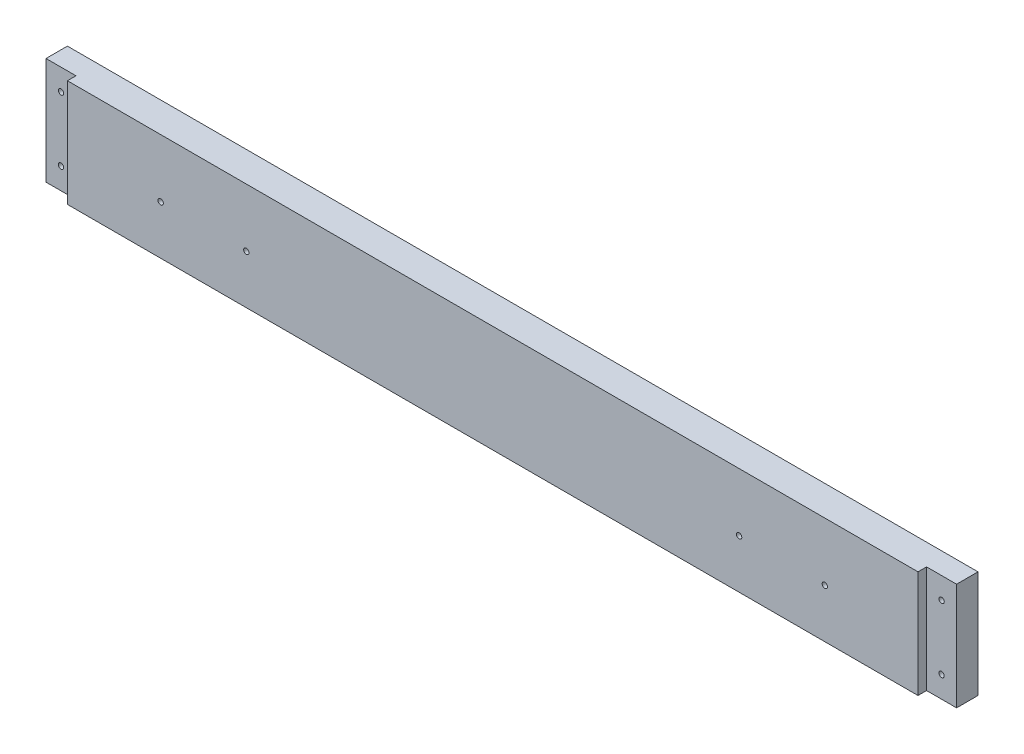
SolidWorks part; units mm, degrees
material "Pine"
ref_plane "Front Plane" through (0, 0, 0) normal (0, 0, 1) x (1, 0, 0)
ref_plane "Top Plane" through (0, 0, 0) normal (0, 1, 0) x (1, 0, 0)
ref_plane "Right Plane" through (0, 0, 0) normal (1, 0, 0) x (0, 0, -1)
sketch "Sketch1" plane through (0, 0, 0) normal (0, 0, 1) x (1, 0, 0)
  line L0 (8932.6508, -5243.5125) -> (10226.1458, -5243.5125)
  line L1 (9086.3208, -4722.0918) -> (10222.9708, -4853.7812)
  line L2 (8914.8708, -6342.0625) -> (10197.5708, -6342.0625)
  line L3 (8914.8708, -5808.6625) -> (10197.5708, -5808.6625)
  line L4 (8919.6333, -5253.0375) -> (10218.2083, -5253.0375)
  line L5 (9134.2633, -4656.1375) -> (9134.2633, -4638.3575)
  line L6 (9091.0833, -4638.3575) -> (9134.2633, -4638.3575)
  line L7 (9091.0833, -4567.2375) -> (9091.0833, -4638.3575)
  line L8 (9134.2633, -4656.1375) -> (9581.3033, -4656.1375)
  line L9 (9091.0833, -4567.2375) -> (9624.4833, -4567.2375)
  line L10 (9581.3033, -4656.1375) -> (9581.3033, -4638.3575)
  line L11 (9581.3033, -4638.3575) -> (9624.4833, -4638.3575)
  line L12 (9624.4833, -4567.2375) -> (9624.4833, -4638.3575)
  line L13 (8932.6508, -5225.7325) -> (9344.9775, -5225.7325)
  line L14 (8932.6508, -5256.2125) -> (8932.6508, -5243.5125)
  line L15 (8911.6958, -5256.2125) -> (8932.6508, -5256.2125)
  line L16 (8914.8708, -4722.0918) -> (9086.3208, -4722.0918)
  line L17 (8911.6958, -4715.5913) -> (8932.6508, -4715.5913)
  line L18 (8914.8708, -6342.0625) -> (8914.8708, -5808.6625)
  line L19 (12082.9917, -4722.0918) -> (10946.3417, -4853.7812)
  line L20 (12236.6617, -5243.5125) -> (10943.1667, -5243.5125)
  line L21 (10951.1042, -5253.0375) -> (12249.6792, -5253.0375)
  line L22 (10838.3917, -5656.2625) -> (11308.2917, -5656.2625)
  line L23 (10838.3917, -5719.7625) -> (11308.2917, -5719.7625)
  line L24 (10838.3917, -5742.5368) -> (11308.2917, -5742.5368)
  line L25 (10806.6417, -6342.0625) -> (11340.0417, -6342.0625)
  line L26 (10803.4667, -6335.7125) -> (11343.2167, -6335.7125)
  line L27 (10803.4667, -6317.9325) -> (11343.2167, -6317.9325)
  line L28 (10943.1667, -5225.7325) -> (11376.4483, -5225.7325)
  line L29 (11506.7292, -4754.5625) -> (10806.6417, -4827.5875)
  line L30 (11506.7292, -4567.2375) -> (11506.7292, -4754.5625)
  line L31 (10806.6417, -4567.2375) -> (10806.6417, -4827.5875)
  line L32 (10806.6417, -4567.2375) -> (11506.7292, -4567.2375)
  line L33 (10235.6708, -6329.3625) -> (10245.1958, -6329.3625)
  line L34 (10245.1958, -6329.3625) -> (10254.7208, -6278.5625)
  line L35 (10302.3458, -6329.3625) -> (10311.8708, -6278.5625)
  line L36 (10302.3458, -6329.3625) -> (10292.8208, -6329.3625)
  line L37 (10245.1958, -5821.3625) -> (10254.7208, -5872.1625)
  line L38 (10235.6708, -5821.3625) -> (10245.1958, -5821.3625)
  line L39 (10292.8208, -5821.3625) -> (10302.3458, -5821.3625)
  line L40 (10302.3458, -5821.3625) -> (10311.8708, -5872.1625)
  line L41 (10235.6708, -5821.3625) -> (10235.6708, -6329.3625)
  line L42 (10254.7208, -5872.1625) -> (10254.7208, -6278.5625)
  line L43 (10311.8708, -5872.1625) -> (10311.8708, -6278.5625)
  line L44 (10292.8208, -5821.3625) -> (10292.8208, -6329.3625)
  line L45 (8932.6508, -5225.7325) -> (8932.6508, -4715.5913)
  line L46 (8911.6958, -4715.5913) -> (8911.6958, -5256.2125)
  line L47 (8914.8708, -5248.275) -> (8914.8708, -4722.0918)
  line L48 (8919.6333, -5253.0375) -> (8914.8708, -5248.275)
  line L49 (8914.8708, -5145.0875) -> (8937.426, -5145.0875)
  line L50 (8914.8708, -5202.2375) -> (8937.426, -5202.2375)
  line L51 (10838.3917, -5656.2625) -> (10838.3917, -5719.7625)
  line L52 (10832.0417, -5736.1868) -> (10856.1717, -5736.1868)
  line L53 (10806.6417, -6342.0625) -> (10806.6417, -5818.7368)
  line L54 (10832.0417, -5649.9125) -> (10856.1717, -5649.9125)
  line L55 (10832.0417, -5726.1125) -> (10856.1717, -5726.1125)
  line L56 (10806.6417, -5818.7368) -> (10833.9015, -5818.7368)
  line L57 (10832.0417, -5806.0442) -> (10851.6815, -5806.0442)
  line L58 (10856.1717, -5801.5541) -> (10856.1717, -5736.1868)
  line L59 (10838.3917, -5814.2467) -> (10838.3917, -5742.5368)
  line L60 (10832.0417, -5806.0442) -> (10832.0417, -5736.1868)
  line L61 (10803.4667, -6317.9325) -> (10803.4667, -6335.7125)
  line L62 (10197.5708, -5808.6625) -> (10197.5708, -6342.0625)
  line L63 (9762.3842, -6348.4125) -> (9762.3842, -5802.3125)
  line L64 (9780.1642, -6348.4125) -> (9762.3842, -6348.4125)
  line L65 (9780.1642, -5802.3125) -> (9780.1642, -6348.4125)
  line L66 (9762.3842, -5802.3125) -> (9780.1642, -5802.3125)
  line L67 (9332.2775, -6348.4125) -> (9332.2775, -5802.3125)
  line L68 (9332.2775, -6348.4125) -> (9350.0575, -6348.4125)
  line L69 (9350.0575, -5802.3125) -> (9350.0575, -6348.4125)
  line L70 (9332.2775, -5802.3125) -> (9350.0575, -5802.3125)
  line L71 (9993.8374, -6061.075) -> (9993.8374, -6045.2418)
  line L72 (9998.5999, -6065.8375) -> (10014.4331, -6065.8375)
  line L73 (9998.5999, -6084.8875) -> (10014.4331, -6084.8875)
  line L74 (9993.8374, -6105.4832) -> (9993.8374, -6089.65)
  line L75 (9974.7874, -6105.4832) -> (9974.7874, -6089.65)
  line L76 (9954.1917, -6084.8875) -> (9970.0249, -6084.8875)
  line L77 (9974.7874, -6061.075) -> (9974.7874, -6045.2418)
  line L78 (9954.1917, -6065.8375) -> (9970.0249, -6065.8375)
  line L79 (10793.9417, -6237.2875) -> (10816.4969, -6237.2875)
  line L80 (10793.9417, -6294.4375) -> (10816.4969, -6294.4375)
  line L81 (10856.1717, -5649.9125) -> (10856.1717, -5726.1125)
  line L82 (10832.0417, -5726.1125) -> (10832.0417, -5649.9125)
  line L83 (10226.1458, -5225.7325) -> (10226.1458, -5243.5125)
  line L84 (10205.1908, -5257.8) -> (10205.1908, -4844.2499)
  line L85 (10230.9083, -4844.2499) -> (10230.9083, -5257.8)
  line L86 (10205.1908, -5257.8) -> (10230.9083, -5257.8)
  line L87 (10205.1908, -4844.2499) -> (10230.9083, -4844.2499)
  line L88 (10946.3417, -5176.8375) -> (10968.8969, -5176.8375)
  line L89 (9349.4676, -5141.9125) -> (9358.2674, -5141.9125)
  line L90 (10946.3417, -5119.6875) -> (10968.8969, -5119.6875)
  line L91 (9929.011, -4660.9635) -> (10066.0807, -4660.9635)
  line L92 (9929.011, -4678.7435) -> (10066.0807, -4678.7435)
  line L93 (10943.1667, -5225.7325) -> (10943.1667, -5243.5125)
  line L94 (10946.3417, -5248.275) -> (10951.1042, -5253.0375)
  line L95 (10946.3417, -5257.8063) -> (10946.3417, -4849.0188)
  line L96 (10964.1217, -5257.8) -> (10964.1217, -4844.2499)
  line L97 (10938.4042, -4844.2499) -> (10938.4042, -5257.8)
  line L98 (10938.4042, -5257.8) -> (10964.1217, -5257.8)
  line L99 (10964.1217, -4844.2499) -> (10938.4042, -4844.2499)
  line L100 (10344.8908, -4560.8875) -> (10369.0208, -4560.8875)
  line L101 (10344.8908, -4560.8875) -> (10369.0208, -4560.8875)
  line L102 (10800.2917, -4560.8875) -> (10824.4217, -4560.8875)
  line L103 (10200.4156, -5119.6875) -> (10222.9708, -5119.6875)
  line L104 (10200.4156, -5176.8375) -> (10222.9708, -5176.8375)
  line L105 (9344.9775, -5146.4026) -> (9344.9775, -5225.7325)
  line L106 (10344.8908, -4560.8875) -> (10344.8908, -4833.9375)
  line L107 (9792.8642, -5225.7325) -> (9792.8642, -5146.4026)
  line L108 (9362.7575, -5225.7325) -> (9775.0842, -5225.7325)
  line L109 (9680.3633, -4761.8396) -> (9680.3633, -4559.9604)
  line L110 (9656.2333, -4559.9604) -> (9680.3633, -4559.9604)
  line L111 (9656.2333, -4761.8396) -> (9680.3633, -4761.8396)
  line L112 (9656.2333, -4761.8396) -> (9656.2333, -4559.9604)
  line L113 (9779.5743, -5141.9125) -> (9788.374, -5141.9125)
  line L114 (10070.5708, -4665.4536) -> (10070.5708, -4674.2534)
  line L115 (9924.5208, -4674.2534) -> (9924.5208, -4665.4536)
  line L116 (12127.4417, -6188.3925) -> (12205.5015, -6188.3925)
  line L117 (12209.9917, -6170.6125) -> (12209.9917, -6183.9024)
  line L118 (9792.8642, -5225.7325) -> (10226.1458, -5225.7325)
  line L119 (9662.5833, -4754.5625) -> (10362.6708, -4827.5875)
  line L120 (9662.5833, -4567.2375) -> (9662.5833, -4754.5625)
  line L121 (10362.6708, -4567.2375) -> (10362.6708, -4827.5875)
  line L122 (9662.5833, -4567.2375) -> (10362.6708, -4567.2375)
  line L123 (10824.4217, -4833.9375) -> (10800.2917, -4833.9375)
  line L124 (10800.2917, -4833.9375) -> (10800.2917, -4560.8875)
  line L125 (10824.4217, -4560.8875) -> (10824.4217, -4833.9375)
  line L126 (10344.8908, -4833.9375) -> (10369.0208, -4833.9375)
  line L127 (10369.0208, -4833.9375) -> (10369.0208, -4560.8875)
  line L128 (10222.9708, -5248.275) -> (10218.2083, -5253.0375)
  line L129 (10222.9708, -5257.8063) -> (10222.9708, -4849.0188)
  line L130 (11734.6544, -5701.375) -> (11739.2301, -5701.375)
  line L131 (9362.7575, -5225.7325) -> (9362.7575, -5146.4026)
  line L132 (9775.0842, -5146.4026) -> (9775.0842, -5225.7325)
  line L133 (11761.3864, -5701.375) -> (11756.8282, -5701.375)
  line L134 (11734.6544, -5693.755) -> (11739.2301, -5693.755)
  line L135 (11761.4039, -5693.755) -> (11756.8282, -5693.755)
  line L136 (11734.6544, -5701.375) -> (11739.2301, -5701.375)
  line L137 (11744.3462, -5721.3024) -> (11744.3462, -5706.4179)
  line L138 (11751.7122, -5721.3024) -> (11751.7122, -5706.4179)
  line L139 (11740.0917, -6170.6125) -> (11740.0917, -6183.9024)
  line L140 (11689.2917, -6188.3925) -> (11822.6417, -6188.3925)
  line L141 (11689.2917, -6348.4093) -> (11689.2917, -6164.2657)
  line L142 (11689.2917, -6164.2657) -> (11746.4417, -6164.2657)
  line L143 (11746.4417, -6164.2657) -> (11746.4417, -6188.3925)
  line L144 (11689.2917, -6164.2657) -> (11746.4417, -6164.2657)
  line L145 (11340.0417, -5818.7368) -> (11340.0417, -6342.0625)
  line L146 (11290.5117, -5726.1125) -> (11314.6417, -5726.1125)
  line L147 (11290.5117, -5649.9125) -> (11290.5117, -5726.1125)
  line L148 (11340.0417, -5818.7368) -> (11312.7818, -5818.7368)
  line L149 (11314.6417, -5806.0442) -> (11295.0018, -5806.0442)
  line L150 (11290.5117, -5801.5541) -> (11290.5117, -5736.1868)
  line L151 (11308.2917, -5814.2467) -> (11308.2917, -5742.5368)
  line L152 (11314.6417, -5806.0442) -> (11314.6417, -5736.1868)
  line L153 (11290.5117, -5736.1868) -> (11314.6417, -5736.1868)
  line L154 (11848.0417, -6267.1325) -> (11962.3417, -6267.1325)
  line L155 (11962.3417, -6267.1325) -> (11962.3417, -6203.6325)
  line L156 (11343.2167, -6317.9325) -> (11343.2167, -6335.7125)
  line L157 (11365.4417, -5656.2625) -> (11365.4417, -5719.7625)
  line L158 (11365.4417, -5656.2625) -> (11479.7417, -5656.2625)
  line L159 (11778.1917, -6071.3937) -> (11802.3217, -6071.3937)
  line L160 (11314.6417, -5726.1125) -> (11314.6417, -5649.9125)
  line L161 (11314.6417, -5649.9125) -> (11290.5117, -5649.9125)
  line L162 (11308.2917, -5719.7625) -> (11308.2917, -5656.2625)
  line L163 (11689.2917, -6348.4093) -> (11713.4217, -6348.4093)
  line L164 (12203.6417, -6164.2657) -> (12260.7917, -6164.2657)
  line L165 (11713.4217, -6348.4093) -> (11713.4217, -6164.2657)
  line L166 (11695.6417, -6342.0625) -> (11695.6417, -6170.6125)
  line L167 (11695.6417, -6048.5337) -> (11699.4517, -6052.3437)
  line L168 (11822.6417, -6292.5325) -> (11822.6417, -6188.3925)
  line L169 (11695.6417, -6342.0625) -> (11695.6417, -6170.6125)
  line L170 (11848.0417, -6203.6325) -> (11962.3417, -6203.6325)
  line L171 (11848.0417, -6203.6325) -> (11848.0417, -6267.1325)
  line L172 (11987.7417, -6267.1325) -> (11987.7417, -6203.6325)
  line L173 (11784.5417, -6077.7437) -> (11784.5417, -6141.2438)
  line L174 (11517.8417, -5656.2625) -> (11632.1417, -5656.2625)
  line L175 (11632.1417, -5656.2625) -> (11632.1417, -5719.7625)
  line L176 (11632.1417, -5719.7625) -> (11517.8417, -5719.7625)
  line L177 (11517.8417, -5719.7625) -> (11517.8417, -5656.2625)
  line L178 (11692.4667, -6028.2137) -> (11692.4667, -6045.9937)
  line L179 (11695.6417, -5979.3188) -> (11718.1969, -5979.3188)
  line L180 (11695.6417, -5922.1687) -> (11718.1969, -5922.1687)
  line L181 (11821.0415, -5722.9375) -> (11821.0415, -5943.6)
  line L182 (11687.7042, -5651.5) -> (11701.9917, -5651.5)
  line L183 (11687.7042, -5651.5) -> (11687.7042, -6055.5251)
  line L184 (11687.7042, -6055.5251) -> (11701.9917, -6055.5251)
  line L185 (11701.9917, -6055.5251) -> (11701.9917, -5651.5)
  line L186 (11695.6417, -6055.2013) -> (11695.6417, -5649.595)
  line L187 (11695.6417, -5656.2625) -> (11695.6417, -6048.5337)
  line L188 (11695.6417, -6170.6125) -> (11740.0917, -6170.6125)
  line L189 (12203.6417, -6164.2657) -> (12203.6417, -6188.3925)
  line L190 (12254.4417, -6342.0625) -> (12254.4417, -6170.6125)
  line L191 (12129.0419, -5943.6) -> (12129.0419, -5722.9375)
  line L192 (12254.4417, -6048.5337) -> (12250.6317, -6052.3437)
  line L193 (12257.6167, -6045.9937) -> (12257.6167, -6028.2137)
  line L194 (12248.0917, -5651.5) -> (12262.3792, -5651.5)
  line L195 (12262.3792, -5651.5) -> (12262.3792, -6055.5251)
  line L196 (12262.3792, -6055.5251) -> (12248.0917, -6055.5251)
  line L197 (12248.0917, -6055.5251) -> (12248.0917, -5651.5)
  line L198 (12254.4417, -6141.2438) -> (12254.4417, -6077.7437)
  line L199 (12236.6617, -6164.2657) -> (12260.7917, -6164.2657)
  line L200 (12102.0417, -6267.1325) -> (11987.7417, -6267.1325)
  line L201 (11330.1865, -6237.2875) -> (11352.7417, -6237.2875)
  line L202 (11330.1865, -6294.4375) -> (11352.7417, -6294.4375)
  line L203 (11474.6617, -5851.8425) -> (11492.4417, -5851.8425)
  line L204 (11474.6617, -5808.6625) -> (11474.6617, -5851.8425)
  line L205 (11403.5417, -5808.6625) -> (11474.6617, -5808.6625)
  line L206 (11492.4417, -5851.8425) -> (11492.4417, -6298.8825)
  line L207 (11403.5417, -6342.0625) -> (11403.5417, -5808.6625)
  line L208 (11474.6617, -6298.8825) -> (11492.4417, -6298.8825)
  line L209 (11474.6617, -6342.0625) -> (11474.6617, -6298.8825)
  line L210 (11403.5417, -6342.0625) -> (11474.6617, -6342.0625)
  line L211 (11619.4417, -5851.8425) -> (11601.6617, -5851.8425)
  line L212 (11601.6617, -5808.6625) -> (11601.6617, -5851.8425)
  line L213 (11530.5417, -5808.6625) -> (11601.6617, -5808.6625)
  line L214 (11619.4417, -5851.8425) -> (11619.4417, -6298.8825)
  line L215 (11530.5417, -6342.0625) -> (11530.5417, -5808.6625)
  line L216 (11619.4417, -6298.8825) -> (11601.6617, -6298.8825)
  line L217 (11601.6617, -6342.0625) -> (11601.6617, -6298.8825)
  line L218 (11530.5417, -6342.0625) -> (11601.6617, -6342.0625)
  line L219 (11479.7417, -5719.7625) -> (11479.7417, -5656.2625)
  line L220 (11365.4417, -5719.7625) -> (11479.7417, -5719.7625)
  line L221 (11778.1917, -6147.5937) -> (11802.3217, -6147.5937)
  line L222 (11802.3217, -6071.3937) -> (11802.3217, -6147.5937)
  line L223 (11778.1917, -6147.5937) -> (11778.1917, -6071.3937)
  line L224 (12254.4417, -5922.1687) -> (12231.8865, -5922.1687)
  line L225 (12254.4417, -5979.3188) -> (12231.8865, -5979.3188)
  line L226 (12254.4417, -6055.2013) -> (12254.4417, -5649.595)
  line L227 (12254.4417, -6048.5337) -> (12254.4417, -5656.2625)
  line L228 (11841.6917, -5702.2873) -> (12108.3917, -5702.2873)
  line L229 (11822.6417, -6292.5325) -> (12127.4417, -6292.5325)
  line L230 (12127.4417, -6292.5325) -> (12127.4417, -6188.3925)
  line L231 (12254.4417, -6170.6125) -> (12209.9917, -6170.6125)
  line L232 (11695.6417, -6342.0625) -> (12254.4417, -6342.0625)
  line L233 (12236.6617, -6348.4093) -> (12260.7917, -6348.4093)
  line L234 (12260.7917, -6348.4093) -> (12260.7917, -6164.2657)
  line L235 (12236.6617, -6348.4093) -> (12236.6617, -6164.2657)
  line L236 (12102.0417, -6203.6325) -> (12102.0417, -6267.1325)
  line L237 (11987.7417, -6203.6325) -> (12102.0417, -6203.6325)
  line L238 (12236.6617, -6147.5937) -> (12236.6617, -6071.3937)
  line L239 (12203.6417, -6188.3925) -> (12260.7917, -6188.3925)
  line L240 (11098.7417, -4665.4536) -> (11098.7417, -4674.2534)
  line L241 (11394.2283, -5146.4026) -> (11394.2283, -5225.7325)
  line L242 (11376.4483, -5225.7325) -> (11376.4483, -5146.4026)
  line L243 (11394.2283, -5225.7325) -> (11806.555, -5225.7325)
  line L244 (11841.6917, -5964.2502) -> (12108.3917, -5964.2502)
  line L245 (12236.6617, -6147.5937) -> (12260.7917, -6147.5937)
  line L246 (12236.6617, -5256.2125) -> (12236.6617, -5243.5125)
  line L247 (12260.7917, -6147.5937) -> (12260.7917, -6071.3937)
  line L248 (12260.7917, -6071.3937) -> (12236.6617, -6071.3937)
  line L249 (12254.4417, -6077.7437) -> (11784.5417, -6077.7437)
  line L250 (11784.5417, -6141.2438) -> (12254.4417, -6141.2438)
  line L252 (12254.4417, -5656.2625) -> (11695.6417, -5656.2625)
  line L253 (11699.4517, -6052.3437) -> (12250.6317, -6052.3437)
  line L254 (11692.4667, -6045.9937) -> (12257.6167, -6045.9937)
  line L255 (11692.4667, -6028.2137) -> (12257.6167, -6028.2137)
  line L256 (11824.335, -5146.4026) -> (11824.335, -5225.7325)
  line L257 (11811.0451, -5141.9125) -> (11819.8449, -5141.9125)
  line L258 (11244.7917, -4674.2534) -> (11244.7917, -4665.4536)
  line L259 (11806.555, -5225.7325) -> (11806.555, -5146.4026)
  line L260 (11488.9492, -4761.8396) -> (11488.9492, -4559.9604)
  line L261 (11488.9492, -4559.9604) -> (11513.0792, -4559.9604)
  line L262 (11488.9492, -4761.8396) -> (11513.0792, -4761.8396)
  line L263 (11513.0792, -4761.8396) -> (11513.0792, -4559.9604)
  line L264 (11240.3015, -4660.9635) -> (11103.2318, -4660.9635)
  line L265 (11103.2318, -4678.7435) -> (11240.3015, -4678.7435)
  line L266 (12236.6617, -5225.7325) -> (12236.6617, -4715.5913)
  line L267 (12257.6167, -4715.5913) -> (12257.6167, -5256.2125)
  line L268 (12254.4417, -5248.275) -> (12254.4417, -4722.0918)
  line L269 (12236.6617, -5225.7325) -> (11824.335, -5225.7325)
  line L270 (12035.0492, -4656.1375) -> (12035.0492, -4638.3575)
  line L271 (12078.2292, -4638.3575) -> (12035.0492, -4638.3575)
  line L272 (12078.2292, -4567.2375) -> (12078.2292, -4638.3575)
  line L273 (12035.0492, -4656.1375) -> (11588.0092, -4656.1375)
  line L274 (11544.8292, -4567.2375) -> (12078.2292, -4567.2375)
  line L275 (11588.0092, -4656.1375) -> (11588.0092, -4638.3575)
  line L276 (11544.8292, -4638.3575) -> (11588.0092, -4638.3575)
  line L277 (11544.8292, -4567.2375) -> (11544.8292, -4638.3575)
  line L278 (12249.6792, -5253.0375) -> (12254.4417, -5248.275)
  line L280 (12257.6167, -5256.2125) -> (12236.6617, -5256.2125)
  line L281 (12231.8865, -5145.0875) -> (12254.4417, -5145.0875)
  line L282 (12231.8865, -5202.2375) -> (12254.4417, -5202.2375)
  line L283 (12236.6617, -4715.5913) -> (12257.6167, -4715.5913)
  line L284 (12082.9917, -4722.0918) -> (12254.4417, -4722.0918)
  line L285 (11380.9385, -5141.9125) -> (11389.7382, -5141.9125)
  circle A0 centre (8923.7608, -4778.9042) radius 1.5875
  circle A1 centre (9062.6598, -4736.3765) radius 2.3685
  circle A2 centre (9051.3958, -6281.7375) radius 22.225
  circle A3 centre (9083.1458, -6249.9875) radius 1.5875
  circle A4 centre (9083.1458, -6313.4875) radius 1.5875
  circle A5 centre (9019.6458, -6249.9875) radius 1.5875
  circle A6 centre (9019.6458, -6313.4875) radius 1.5875
  circle A7 centre (8972.3383, -5202.2375) radius 1.5875
  circle A8 centre (8923.7608, -5015.9708) radius 1.5875
  circle A9 centre (8923.7608, -5134.5042) radius 1.5875
  circle A10 centre (9054.5708, -5234.6225) radius 1.5875
  circle A11 centre (8923.7608, -4897.4375) radius 1.5875
  circle A12 centre (8972.3383, -5087.9375) radius 1.5875
  circle A13 centre (8972.3383, -5145.0875) radius 1.5875
  circle A14 centre (10847.2817, -5668.9625) radius 1.5875
  circle A15 centre (10847.2817, -5707.0625) radius 1.5875
  circle A16 centre (10847.2817, -5755.2368) radius 1.5875
  circle A17 centre (10851.4092, -6237.2875) radius 1.5875
  circle A18 centre (10851.4092, -6294.4375) radius 1.5875
  circle A19 centre (10847.2817, -5793.3442) radius 1.5875
  arc A20 (10833.9015, -5818.7368) -> (10838.3917, -5814.2467) centre (10836.1466, -5816.4918) ccw
  arc A21 (10851.6815, -5806.0442) -> (10856.1717, -5801.5541) centre (10853.9266, -5803.7992) ccw
  circle A22 centre (10882.8417, -6040.4375) radius 1.5875
  circle A23 centre (10882.8417, -6218.2375) radius 1.5875
  circle A24 centre (10882.8417, -5862.6375) radius 1.5875
  circle A25 centre (10908.2417, -6326.8225) radius 1.5875
  circle A26 centre (10908.2417, -6326.8225) radius 1.5875
  circle A27 centre (10851.4092, -6180.1375) radius 1.5875
  circle A28 centre (10815.5317, -4783.4231) radius 1.5875
  circle A29 centre (10815.5317, -4696.9488) radius 1.5875
  circle A30 centre (10815.5317, -4610.4746) radius 1.5875
  circle A31 centre (10979.1323, -4867.0082) radius 2.3685
  circle A32 centre (10190.1802, -4867.0082) radius 2.3685
  circle A33 centre (10955.2317, -4929.9812) radius 1.5875
  circle A34 centre (10955.2317, -5031.5812) radius 1.5875
  circle A35 centre (10214.0808, -4929.9812) radius 1.5875
  circle A36 centre (10214.0808, -5031.5812) radius 1.5875
  circle A37 centre (9341.1675, -6265.8625) radius 1.5875
  circle A38 centre (9771.2742, -5884.8625) radius 1.5875
  circle A39 centre (9771.2742, -6138.8625) radius 1.5875
  circle A40 centre (9771.2742, -6011.8625) radius 1.5875
  arc A41 (10036.2287, -6113.8083) -> (10051.3426, -6111.6033) centre (10042.9639, -6107.0732) ccw
  arc A42 (10051.3426, -6111.6033) -> (10051.3426, -6039.1217) centre (9984.3124, -6075.3625) ccw
  arc A43 (10051.3426, -6039.1217) -> (10036.2287, -6036.9167) centre (10042.9639, -6043.6518) ccw
  arc A44 (10034.5851, -6102.5431) -> (10034.5851, -6048.1819) centre (9984.3124, -6075.3625) ccw
  arc A45 (10034.5851, -6102.5431) -> (10036.2287, -6113.8083) centre (10042.9639, -6107.0732) ccw
  arc A46 (10036.2287, -6036.9167) -> (10034.5851, -6048.1819) centre (10042.9639, -6043.6518) ccw
  arc A47 (9945.8666, -6127.2787) -> (9948.0717, -6142.3927) centre (9952.6018, -6134.0139) ccw
  arc A48 (9948.0717, -6142.3927) -> (10020.5532, -6142.3927) centre (9984.3124, -6075.3625) ccw
  arc A49 (10020.5532, -6142.3927) -> (10022.7583, -6127.2787) centre (10016.0231, -6134.0139) ccw
  arc A50 (9957.1319, -6125.6352) -> (10011.493, -6125.6352) centre (9984.3124, -6075.3625) ccw
  arc A51 (9957.1319, -6125.6352) -> (9945.8666, -6127.2787) centre (9952.6018, -6134.0139) ccw
  arc A52 (10022.7583, -6127.2787) -> (10011.493, -6125.6352) centre (10016.0231, -6134.0139) ccw
  arc A53 (9932.3962, -6036.9167) -> (9917.2822, -6039.1217) centre (9925.661, -6043.6518) ccw
  arc A54 (9917.2822, -6039.1217) -> (9917.2822, -6111.6033) centre (9984.3124, -6075.3625) ccw
  arc A55 (9917.2822, -6111.6033) -> (9932.3962, -6113.8083) centre (9925.661, -6107.0732) ccw
  arc A56 (9934.0398, -6048.1819) -> (9934.0398, -6102.5431) centre (9984.3124, -6075.3625) ccw
  arc A57 (9934.0398, -6048.1819) -> (9932.3962, -6036.9167) centre (9925.661, -6043.6518) ccw
  arc A58 (9932.3962, -6113.8083) -> (9934.0398, -6102.5431) centre (9925.661, -6107.0732) ccw
  arc A59 (9945.8666, -6023.4463) -> (9957.1319, -6025.0898) centre (9952.6018, -6016.7111) ccw
  arc A60 (10011.493, -6025.0898) -> (10022.7583, -6023.4463) centre (10016.0231, -6016.7111) ccw
  arc A61 (10011.493, -6025.0898) -> (9957.1319, -6025.0898) centre (9984.3124, -6075.3625) ccw
  arc A62 (9948.0717, -6008.3323) -> (9945.8666, -6023.4463) centre (9952.6018, -6016.7111) ccw
  arc A63 (10020.5532, -6008.3323) -> (9948.0717, -6008.3323) centre (9984.3124, -6075.3625) ccw
  arc A64 (10022.7583, -6023.4463) -> (10020.5532, -6008.3323) centre (10016.0231, -6016.7111) ccw
  arc A65 (10005.0943, -6187.7574) -> (10096.7073, -6096.1443) centre (9984.3124, -6075.3625) ccw
  arc A66 (9993.8374, -6178.3911) -> (10005.0943, -6187.7574) centre (10003.3624, -6178.3911) ccw
  arc A67 (10001.6306, -6169.0249) -> (10077.9748, -6092.6807) centre (9984.3124, -6075.3625) ccw
  arc A68 (10087.3411, -6084.8875) -> (10077.9748, -6092.6807) centre (10087.3411, -6094.4125) ccw
  arc A69 (10001.6306, -6169.0249) -> (9993.8374, -6178.3911) centre (10003.3624, -6178.3911) ccw
  arc A70 (9963.5306, -6187.7574) -> (9974.7874, -6178.3911) centre (9965.2624, -6178.3911) ccw
  arc A71 (9871.9176, -6096.1443) -> (9963.5306, -6187.7574) centre (9984.3124, -6075.3625) ccw
  arc A72 (9881.2838, -6084.8875) -> (9871.9176, -6096.1443) centre (9881.2838, -6094.4125) ccw
  arc A73 (9890.65, -6092.6807) -> (9966.9943, -6169.0249) centre (9984.3124, -6075.3625) ccw
  arc A74 (9974.7874, -6178.3911) -> (9966.9943, -6169.0249) centre (9965.2624, -6178.3911) ccw
  arc A75 (9890.65, -6092.6807) -> (9881.2838, -6084.8875) centre (9881.2838, -6094.4125) ccw
  arc A76 (9871.9176, -6054.5807) -> (9881.2838, -6065.8375) centre (9881.2838, -6056.3125) ccw
  arc A77 (9963.5306, -5962.9676) -> (9871.9176, -6054.5807) centre (9984.3124, -6075.3625) ccw
  arc A78 (9974.7874, -5972.3339) -> (9963.5306, -5962.9676) centre (9965.2624, -5972.3339) ccw
  arc A79 (9966.9943, -5981.7001) -> (9890.65, -6058.0443) centre (9984.3124, -6075.3625) ccw
  arc A80 (9881.2838, -6065.8375) -> (9890.65, -6058.0443) centre (9881.2838, -6056.3125) ccw
  arc A81 (9966.9943, -5981.7001) -> (9974.7874, -5972.3339) centre (9965.2624, -5972.3339) ccw
  arc A82 (10077.9748, -6058.0443) -> (10087.3411, -6065.8375) centre (10087.3411, -6056.3125) ccw
  arc A83 (9993.8374, -5972.3339) -> (10001.6306, -5981.7001) centre (10003.3624, -5972.3339) ccw
  arc A84 (10077.9748, -6058.0443) -> (10001.6306, -5981.7001) centre (9984.3124, -6075.3625) ccw
  arc A85 (10087.3411, -6065.8375) -> (10096.7073, -6054.5807) centre (10087.3411, -6056.3125) ccw
  arc A86 (10096.7073, -6054.5807) -> (10005.0943, -5962.9676) centre (9984.3124, -6075.3625) ccw
  arc A87 (10005.0943, -5962.9676) -> (9993.8374, -5972.3339) centre (10003.3624, -5972.3339) ccw
  arc A88 (10014.4331, -6065.8375) -> (10018.7361, -6059.0339) centre (10014.4331, -6061.075) ccw
  arc A89 (10018.7361, -6059.0339) -> (10000.641, -6040.9388) centre (9984.3124, -6075.3625) ccw
  arc A90 (10000.641, -6040.9388) -> (9993.8374, -6045.2418) centre (9998.5999, -6045.2418) ccw
  arc A91 (9993.8374, -6061.075) -> (9998.5999, -6065.8375) centre (9998.5999, -6061.075) ccw
  arc A92 (9993.8374, -6105.4832) -> (10000.641, -6109.7862) centre (9998.5999, -6105.4832) ccw
  arc A93 (10000.641, -6109.7862) -> (10018.7361, -6091.6911) centre (9984.3124, -6075.3625) ccw
  arc A94 (10018.7361, -6091.6911) -> (10014.4331, -6084.8875) centre (10014.4331, -6089.65) ccw
  arc A95 (9998.5999, -6084.8875) -> (9993.8374, -6089.65) centre (9998.5999, -6089.65) ccw
  arc A96 (9954.1917, -6084.8875) -> (9949.8888, -6091.6911) centre (9954.1917, -6089.65) ccw
  arc A97 (9949.8888, -6091.6911) -> (9967.9839, -6109.7862) centre (9984.3124, -6075.3625) ccw
  arc A98 (9967.9839, -6109.7862) -> (9974.7874, -6105.4832) centre (9970.0249, -6105.4832) ccw
  arc A99 (9974.7874, -6089.65) -> (9970.0249, -6084.8875) centre (9970.0249, -6089.65) ccw
  arc A100 (9970.0249, -6065.8375) -> (9974.7874, -6061.075) centre (9970.0249, -6061.075) ccw
  arc A101 (9949.8888, -6059.0339) -> (9954.1917, -6065.8375) centre (9954.1917, -6061.075) ccw
  arc A102 (9967.9839, -6040.9388) -> (9949.8888, -6059.0339) centre (9984.3124, -6075.3625) ccw
  arc A103 (9974.7874, -6045.2418) -> (9967.9839, -6040.9388) centre (9970.0249, -6045.2418) ccw
  arc A104 (10096.7073, -6096.1443) -> (10087.3411, -6084.8875) centre (10087.3411, -6094.4125) ccw
  circle A105 centre (9771.2742, -6265.8625) radius 1.5875
  circle A106 centre (9341.1675, -5884.8625) radius 1.5875
  circle A107 centre (9341.1675, -6138.8625) radius 1.5875
  circle A108 centre (9341.1675, -6011.8625) radius 1.5875
  circle A109 centre (11037.2315, -4887.5494) radius 15.0812
  arc A110 (9349.4676, -5141.9125) -> (9344.9775, -5146.4026) centre (9347.2226, -5144.1576) ccw
  arc A111 (9362.7575, -5146.4026) -> (9358.2674, -5141.9125) centre (9360.5124, -5144.1576) ccw
  circle A112 centre (9946.7458, -4669.8535) radius 1.5875
  arc A113 (9924.5208, -4674.2534) -> (9929.011, -4678.7435) centre (9926.7659, -4676.4984) ccw
  circle A114 centre (11003.8092, -5176.8375) radius 1.5875
  circle A115 centre (11003.8092, -5119.6875) radius 1.5875
  circle A116 centre (10353.7808, -4696.9488) radius 1.5875
  circle A117 centre (10353.7808, -4610.4746) radius 1.5875
  circle A118 centre (10353.7808, -4783.4231) radius 1.5875
  circle A119 centre (11003.8092, -5062.5375) radius 1.5875
  circle A120 centre (9353.8675, -5160.9625) radius 1.5875
  circle A121 centre (9638.7708, -5234.6225) radius 1.5875
  circle A122 centre (9671.4733, -4724.1144) radius 1.5875
  circle A123 centre (9671.4733, -4661.3637) radius 1.5875
  circle A124 centre (9671.4733, -4598.6129) radius 1.5875
  arc A125 (9792.8642, -5146.4026) -> (9788.374, -5141.9125) centre (9790.6191, -5144.1576) ccw
  arc A126 (9779.5743, -5141.9125) -> (9775.0842, -5146.4026) centre (9777.3292, -5144.1576) ccw
  circle A127 centre (10048.3458, -4669.8535) radius 1.5875
  arc A128 (10070.5708, -4665.4536) -> (10066.0807, -4660.9635) centre (10068.3258, -4663.2086) ccw
  arc A129 (10066.0807, -4678.7435) -> (10070.5708, -4674.2534) centre (10068.3258, -4676.4984) ccw
  circle A130 centre (9997.5458, -4669.8535) radius 1.5875
  arc A131 (9929.011, -4660.9635) -> (9924.5208, -4665.4536) centre (9926.7659, -4663.2086) ccw
  circle A132 centre (10132.081, -4887.5494) radius 15.0812
  circle A133 centre (10165.5033, -5176.8375) radius 1.5875
  circle A134 centre (10165.5033, -5119.6875) radius 1.5875
  circle A135 centre (9486.3708, -5234.6225) radius 1.5875
  circle A136 centre (10165.5033, -5062.5375) radius 1.5875
  circle A137 centre (9206.9708, -5234.6225) radius 1.5875
  circle A138 centre (10070.5708, -5234.6225) radius 1.5875
  circle A139 centre (9918.1708, -5234.6225) radius 1.5875
  circle A140 centre (9783.9742, -5160.9625) radius 1.5875
  circle A141 centre (9783.9742, -5193.9825) radius 1.5875
  circle A142 centre (9353.8675, -5193.9825) radius 1.5875
  circle A143 centre (11073.3417, -6326.8225) radius 1.5875
  circle A144 centre (11073.3417, -6326.8225) radius 1.5875
  circle A145 centre (11295.2742, -6180.1375) radius 1.5875
  circle A146 centre (11295.2742, -6294.4375) radius 1.5875
  circle A147 centre (11295.2742, -6237.2875) radius 1.5875
  circle A148 centre (11975.0417, -5692.775) radius 3.4925
  circle A149 centre (11263.8417, -5862.6375) radius 1.5875
  arc A150 (11739.2301, -5701.375) -> (11744.3462, -5706.4179) centre (11748.0292, -5697.565) ccw
  arc A151 (11751.7122, -5706.4179) -> (11756.8282, -5701.375) centre (11748.0292, -5697.565) ccw
  arc A152 (11744.3462, -5721.3024) -> (11751.7122, -5721.3024) centre (11748.0292, -5725.505) ccw
  arc A153 (11734.6544, -5693.755) -> (11724.9787, -5697.565) centre (11730.5667, -5697.565) ccw
  arc A154 (11756.8282, -5693.755) -> (11739.2301, -5693.755) centre (11748.0292, -5697.565) ccw
  arc A155 (11724.9787, -5697.565) -> (11734.6544, -5701.375) centre (11730.5667, -5697.565) ccw
  arc A156 (11761.3864, -5701.375) -> (11771.0797, -5697.565) centre (11765.4842, -5697.565) ccw
  arc A157 (11771.0797, -5697.565) -> (11761.4039, -5693.755) centre (11765.4917, -5697.565) ccw
  arc A158 (11740.0917, -6183.9024) -> (11744.5818, -6188.3925) centre (11742.3367, -6186.1474) ccw
  arc A159 (12205.5015, -6188.3925) -> (12209.9917, -6183.9024) centre (12207.7466, -6186.1474) ccw
  circle A160 centre (11299.4017, -5793.3442) radius 1.5875
  arc A161 (11308.2917, -5814.2467) -> (11312.7818, -5818.7368) centre (11310.5367, -5816.4918) ccw
  arc A162 (11290.5117, -5801.5541) -> (11295.0018, -5806.0442) centre (11292.7567, -5803.7992) ccw
  circle A163 centre (11704.5317, -6314.149) radius 1.5875
  circle A164 centre (11748.9817, -6208.7125) radius 1.5875
  circle A165 centre (11263.8417, -6218.2375) radius 1.5875
  circle A166 centre (11263.8417, -6040.4375) radius 1.5875
  circle A167 centre (11238.4417, -6326.8225) radius 1.5875
  circle A168 centre (11238.4417, -6326.8225) radius 1.5875
  circle A169 centre (11299.4017, -5668.9625) radius 1.5875
  circle A170 centre (11299.4017, -5707.0625) radius 1.5875
  circle A171 centre (11726.7567, -6179.5025) radius 1.5875
  circle A172 centre (11704.5317, -6199.3198) radius 1.5875
  circle A173 centre (11748.9817, -6272.2125) radius 1.5875
  circle A174 centre (11704.5317, -6256.7344) radius 1.5875
  circle A175 centre (11299.4017, -5755.2368) radius 1.5875
  circle A176 centre (11913.4467, -6301.4225) radius 1.5875
  circle A177 centre (11790.2567, -6301.4225) radius 1.5875
  circle A178 centre (11793.4317, -6128.5437) radius 1.5875
  circle A179 centre (11753.1092, -5865.0188) radius 1.5875
  circle A180 centre (11809.9417, -6037.1038) radius 1.5875
  circle A181 centre (11809.9417, -6037.1038) radius 1.5875
  circle A182 centre (11753.1092, -5922.1687) radius 1.5875
  circle A183 centre (11975.0417, -5973.7625) radius 3.4925
  circle A184 centre (11975.0417, -6037.1038) radius 1.5875
  circle A185 centre (11753.1092, -5979.3188) radius 1.5875
  circle A186 centre (11975.0417, -6037.1038) radius 1.5875
  arc A187 (11841.6917, -5702.2873) -> (11821.0415, -5722.9375) centre (11841.6917, -5722.9375) ccw
  circle A188 centre (11811.5292, -5833.2687) radius 3.4925
  arc A189 (11821.0415, -5943.6) -> (11841.6917, -5964.2502) centre (11841.6917, -5943.6) ccw
  circle A190 centre (12196.9742, -5865.0188) radius 1.5875
  arc A191 (12129.0419, -5722.9375) -> (12108.3917, -5702.2873) centre (12108.3917, -5722.9375) ccw
  circle A192 centre (12036.6367, -6301.4225) radius 1.5875
  circle A193 centre (12159.8267, -6301.4225) radius 1.5875
  circle A194 centre (12138.5542, -5833.2687) radius 3.4925
  circle A195 centre (12197.2917, -5761.0375) radius 15.0812
  circle A196 centre (11793.4317, -6090.4437) radius 1.5875
  circle A197 centre (12196.9742, -5922.1687) radius 1.5875
  arc A198 (12108.3917, -5964.2502) -> (12129.0419, -5943.6) centre (12108.3917, -5943.6) ccw
  circle A199 centre (12196.9742, -5979.3188) radius 1.5875
  circle A200 centre (12201.1017, -6272.2125) radius 1.5875
  circle A201 centre (12245.5517, -6314.149) radius 1.5875
  circle A202 centre (12245.5517, -6256.7344) radius 1.5875
  circle A203 centre (12201.1017, -6208.7125) radius 1.5875
  circle A204 centre (12223.3267, -6179.5025) radius 1.5875
  circle A205 centre (12245.5517, -6199.3198) radius 1.5875
  circle A206 centre (11171.7667, -4669.8535) radius 1.5875
  circle A207 centre (11222.5667, -4669.8535) radius 1.5875
  arc A208 (11240.3015, -4678.7435) -> (11244.7917, -4674.2534) centre (11242.5466, -4676.4984) ccw
  circle A209 centre (11385.3383, -5193.9825) radius 1.5875
  circle A210 centre (12106.6527, -4736.3765) radius 2.3685
  circle A211 centre (12140.1417, -6037.1038) radius 1.5875
  circle A212 centre (12140.1417, -6037.1038) radius 1.5875
  circle A213 centre (12245.5517, -6090.4437) radius 1.5875
  circle A214 centre (12245.5517, -6128.5437) radius 1.5875
  circle A215 centre (11385.3383, -5160.9625) radius 1.5875
  arc A216 (11824.335, -5146.4026) -> (11819.8449, -5141.9125) centre (11822.0899, -5144.1576) ccw
  arc A217 (11811.0451, -5141.9125) -> (11806.555, -5146.4026) centre (11808.8001, -5144.1576) ccw
  circle A218 centre (11815.445, -5193.9825) radius 1.5875
  circle A219 centre (11815.445, -5160.9625) radius 1.5875
  circle A220 centre (11530.5417, -5234.6225) radius 1.5875
  circle A221 centre (11962.3417, -5234.6225) radius 1.5875
  arc A222 (11244.7917, -4665.4536) -> (11240.3015, -4660.9635) centre (11242.5466, -4663.2086) ccw
  circle A223 centre (11682.9417, -5234.6225) radius 1.5875
  circle A224 centre (11497.8392, -4724.1144) radius 1.5875
  circle A225 centre (11497.8392, -4661.3637) radius 1.5875
  circle A226 centre (11497.8392, -4598.6129) radius 1.5875
  circle A227 centre (11120.9667, -4669.8535) radius 1.5875
  arc A228 (11103.2318, -4660.9635) -> (11098.7417, -4665.4536) centre (11100.9867, -4663.2086) ccw
  arc A229 (11098.7417, -4674.2534) -> (11103.2318, -4678.7435) centre (11100.9867, -4676.4984) ccw
  circle A230 centre (12196.9742, -5202.2375) radius 1.5875
  circle A231 centre (12245.5517, -5015.9708) radius 1.5875
  circle A232 centre (12245.5517, -5134.5042) radius 1.5875
  circle A233 centre (12114.7417, -5234.6225) radius 1.5875
  circle A234 centre (12245.5517, -4897.4375) radius 1.5875
  circle A235 centre (12245.5517, -4778.9042) radius 1.5875
  circle A236 centre (12196.9742, -5087.9375) radius 1.5875
  circle A237 centre (12196.9742, -5145.0875) radius 1.5875
  circle A238 centre (11098.7417, -5234.6225) radius 1.5875
  circle A239 centre (11251.1417, -5234.6225) radius 1.5875
  arc A240 (11380.9385, -5141.9125) -> (11376.4483, -5146.4026) centre (11378.6934, -5144.1576) ccw
  arc A241 (11394.2283, -5146.4026) -> (11389.7382, -5141.9125) centre (11391.9833, -5144.1576) ccw
sketch "Sketch2" plane through (0, 0, 0) normal (0, 0, 1) x (1, 0, 0)
  line L0 (11378.1417, -5719.7625) -> (11378.1417, -5656.2625)
  line L1 (11378.1417, -5656.2625) -> (10838.3917, -5656.2625)
  line L2 (10838.3917, -5656.2625) -> (10838.3917, -5719.7625)
  line L3 (10838.3917, -5719.7625) -> (11378.1417, -5719.7625)
  dimension "D1" = 63.5
  dimension "D2" = 539.75
extrude "Extrude1" add sketch "Sketch2" against normal blind 17.78
sketch "Sketch3" plane through (0, 0, 0) normal (0, 0, 1) x (1, 0, 0)
  line L0 (11360.3617, -5656.2625) -> (11378.1417, -5656.2625)
  line L1 (11378.1417, -5656.2625) -> (11378.1417, -5719.7625)
  line L2 (11378.1417, -5719.7625) -> (11360.3617, -5719.7625)
  line L3 (11360.3617, -5719.7625) -> (11360.3617, -5656.2625)
  line L4 (10856.1717, -5656.2625) -> (10856.1717, -5719.7625)
  line L5 (10856.1717, -5719.7625) -> (10838.3917, -5719.7625)
  line L6 (10838.3917, -5719.7625) -> (10838.3917, -5656.2625)
  line L7 (10838.3917, -5656.2625) -> (10856.1717, -5656.2625)
  line L8 (10838.3917, -5719.7625) -> (11378.1417, -5719.7625) construction
  line L9 (11378.1417, -5656.2625) -> (10838.3917, -5656.2625) construction
  dimension "D1" = 17.78
  dimension "D2" = 17.78
extrude "Cut-Extrude1" cut sketch "Sketch3" against normal blind 5.08
sketch "Sketch4" plane through (0, 0, 0) normal (0, 0, 1) x (1, 0, 0)
  line L0 (10838.3917, -5688.0125) -> (10856.1717, -5688.0125) construction
  line L1 (10838.3917, -5656.2625) -> (10838.3917, -5719.7625) construction
  line L2 (10856.1717, -5719.7625) -> (10856.1717, -5656.2625) construction
  line L3 (11378.1417, -5688.0125) -> (11360.3617, -5688.0125) construction
  line L4 (10847.2817, -5688.0125) -> (10847.2817, -5668.9625) construction
  line L5 (10847.2817, -5688.0125) -> (10847.2817, -5707.0625) construction
  line L6 (11378.1417, -5719.7625) -> (11378.1417, -5656.2625) construction
  line L7 (11360.3617, -5656.2625) -> (11360.3617, -5719.7625) construction
  line L8 (11369.2517, -5688.0125) -> (11369.2517, -5668.9625) construction
  line L9 (11369.2517, -5688.0125) -> (11369.2517, -5707.0625) construction
  circle A0 centre (10847.2817, -5668.9625) radius 1.5875
  circle A1 centre (10847.2817, -5707.0625) radius 1.5875
  circle A2 centre (11369.2517, -5707.0625) radius 1.5875
  circle A3 centre (11369.2517, -5668.9625) radius 1.5875
  dimension "D1" = 38.1
  dimension "D2" = 38.1
extrude "Cut-Extrude2" cut sketch "Sketch4" against normal up to surface (17.78 mm away) up to face at (11108.2667, -5688.0125, -17.78)
sketch "Sketch5" plane through (0, 0, -17.78) normal (0, 0, -1) x (-1, 0, 0)
  circle A0 centre (-10911.4167, -5690.7874) radius 1.5875
  circle A1 centre (-10962.2167, -5690.7874) radius 1.5875
  circle A2 centre (-11254.3167, -5690.7874) radius 1.5875
  circle A3 centre (-11305.1167, -5690.7874) radius 1.5875
extrude "Cut-Extrude3" cut sketch "Sketch5" against normal up to surface (17.78 mm away) up to face at (11108.2667, -5688.0125, 0)
